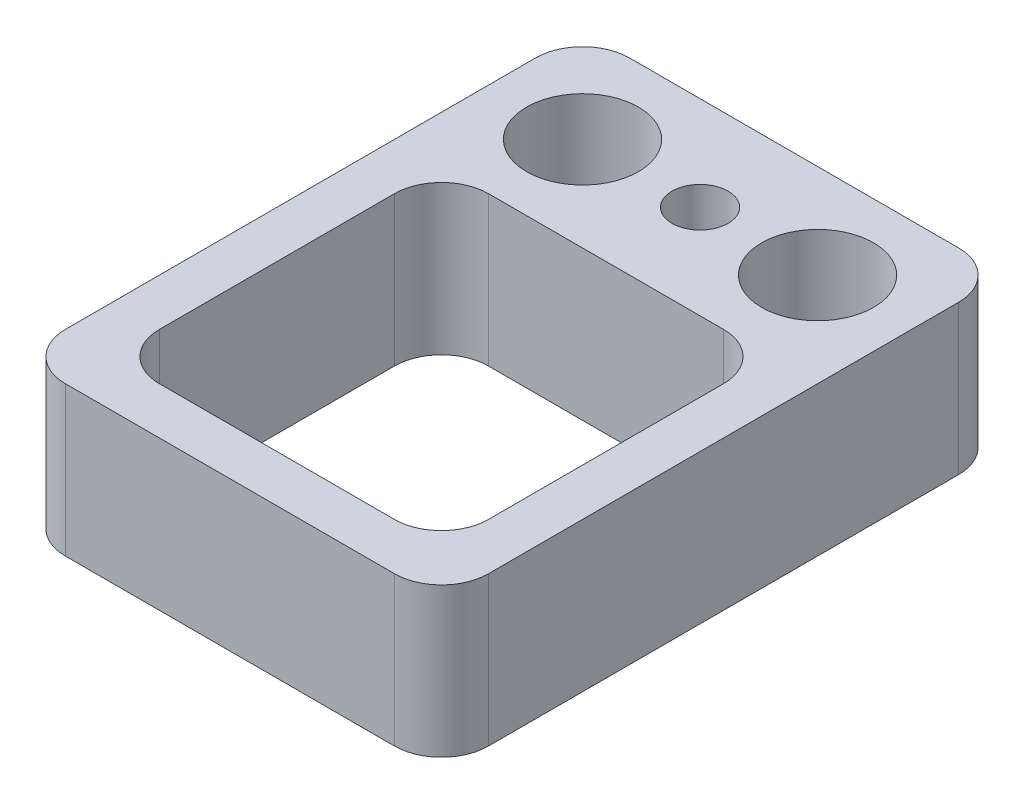
SolidWorks part; units mm, degrees
ref_plane "Front Plane" through (0, 0, 0) normal (0, 0, 1) x (1, 0, 0)
ref_plane "Top Plane" through (0, 0, 0) normal (0, 1, 0) x (1, 0, 0)
ref_plane "Right Plane" through (0, 0, 0) normal (1, 0, 0) x (0, 0, -1)
sketch "Sketch1" plane through (0, 0, 0) normal (0, 1, 0) x (1, 0, 0)
  line L1 (4.5, -6) -> (-4.5, -6)
  line L2 (4.5, -6) -> (4.5, 6)
  line L3 (4.5, 6) -> (-4.5, 6)
  line L4 (-4.5, -6) -> (-4.5, 6)
  line L5 (4.5, -6) -> (-4.5, 6) construction
  line L6 (4.5, 6) -> (-4.5, -6) construction
  point P0 (0, 0)
  dimension "D1" = 9
  dimension "D2" = 12
extrude "Extrude1" add sketch "Sketch1" along normal blind 3.175
sketch "Sketch2" plane through (0, 3.175, 0) normal (0, 1, 0) x (1, 0, 0)
  line L0 (-4.5, 6) -> (-4.5, -6) construction
  line L1 (-3.5, -5) -> (3.5, -5)
  line L2 (-3.5, -5) -> (-3.5, 2)
  line L3 (-3.5, 2) -> (3.5, 2)
  line L4 (3.5, -5) -> (3.5, 2)
  line L5 (-4.5, -6) -> (4.5, -6) construction
  dimension "D1" = 7
  dimension "D2" = 7
  dimension "D3" = 1
  dimension "D4" = 1
extrude "Extrude2" cut sketch "Sketch2" against normal blind 3.5
hole_wizard "#0-80 Tapped Hole1" positions "3DSketch5" profile "Sketch9" tap size "#0-80" standard "Ansi Inch"
sketch3d "3DSketch5"
  line L0 (4.5, 3.175, -6) -> (-4.5, 3.175, -6) construction
  line L1 (4.5, 3.175, 6) -> (4.5, 3.175, -6) construction
  point P0 (0, 3.175, -4)
  dimension "D1" = 2
  dimension "D2" = 4.5
sketch "Sketch9" plane through (0, 3.175, -4) normal (1, 0, 0) x (0, 0, 1)
  line L0 (0, 0) -> (0, 4.3579)
  line L1 (0, 4.3579) -> (0.5956, 4)
  line L2 (0.5956, 4) -> (0.5956, 0)
  line L5 (0.5956, 0) -> (0, 0)
  line L10 (0, 4.3579) -> (-0.5956, 4) construction
  line L11 (0, -6.35) -> (0, 107.95) construction
  dimension "Tap Drill Dia." = 1.1913
  dimension "Tap Drill Depth" = 4
  dimension "Drill Angle" = 118
hole_wizard "3/32 (0.09375) Diameter Hole1" positions "3DSketch6" profile "Sketch10" hole size "3/32" standard "Ansi Inch"
sketch3d "3DSketch6"
  line L0 (4.5, 3.175, -6) -> (-4.5, 3.175, -6) construction
  line L1 (4.5, 3.175, 6) -> (4.5, 3.175, -6) construction
  line L2 (-4.5, 3.175, -6) -> (-4.5, 3.175, 6) construction
  point P0 (-2.5, 3.175, -4)
  point P2 (2.5, 3.175, -4)
  dimension "D1" = 2
  dimension "D2" = 2
  dimension "D3" = 2
  dimension "D4" = 2
sketch "Sketch10" plane through (-2.5, 3.175, -4) normal (1, 0, 0) x (0, 0, 1)
  line L0 (0, 0) -> (0, 10.7154)
  line L1 (0, 10.7154) -> (1.1906, 10)
  line L2 (1.1906, 10) -> (1.1906, 0)
  line L5 (1.1906, 0) -> (0, 0)
  line L10 (0, 10.7154) -> (-1.1906, 10) construction
  line L11 (0, -6.35) -> (0, 107.95) construction
  dimension "Hole Dia." = 2.3812
  dimension "Hole Depth" = 10
  dimension "Drill Angle" = 118
fillet "Fillet7" radius 1 8 edges at (-3.5, 1.5875, 5) (3.5, 1.5875, 5) (3.5, 1.5875, -2) (-3.5, 1.5875, -2) (-4.5, 1.5875, 6) (4.5, 1.5875, 6) (4.5, 1.5875, -6) (-4.5, 1.5875, -6)
